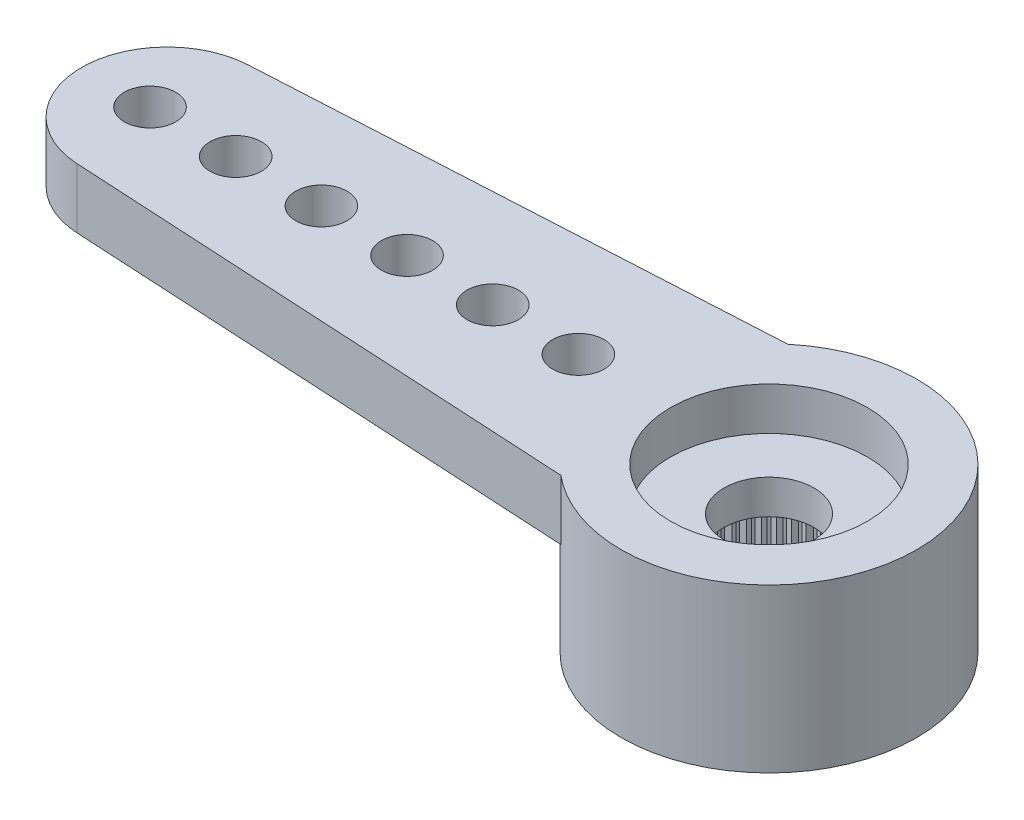
SolidWorks part; units mm, degrees
material "PVC Rígido"
ref_plane "Plano frontal" through (0, 0, 0) normal (0, 0, 1) x (1, 0, 0)
ref_plane "Plano superior" through (0, 0, 0) normal (0, 1, 0) x (1, 0, 0)
ref_plane "Plano direito" through (0, 0, 0) normal (1, 0, 0) x (0, 0, -1)
sketch "Esboço1" plane through (0, 0, 0) normal (0, 1, 0) x (1, 0, 0)
  line L0 (0, 0) -> (-14.05, 0) construction
  line L1 (-14.1591, 1.997) -> (-2.2091, 2.65)
  line L2 (-2.2091, -2.65) -> (-14.1591, -1.997)
  arc A0 (-2.2091, -2.65) -> (-2.2091, 2.65) centre (0, 0) ccw
  arc A1 (-14.1591, 1.997) -> (-14.1591, -1.997) centre (-14.05, 0) ccw
  dimension "D1" = 6.9
  dimension "D2" = 4
  dimension "D3" = 19.5
  dimension "D4" = 5.3
extrude "Ressalto-extrusão1" add sketch "Esboço1" against normal blind 1.4
sketch "Esboço2" plane through (0, -1.4, 0) normal (0, -1, 0) x (1, 0, 0)
  arc A0 (-2.2091, -2.65) -> (-2.2091, 2.65) centre (0, 0) ccw construction
  circle A1 centre (0, 0) radius 3.45
extrude "Ressalto-extrusão2" add sketch "Esboço2" along normal offset from surface (2.4 mm away) 3.8 up to face at (-7.242, 0, 0)
hole_wizard "Furo4" positions "Esboço9" profile "Esboço10" legacy end condition through all
sketch "Esboço9" plane through (0, 0, 0) normal (0, 1, 0) x (1, 0, 0)
  line L1 (-14.45, 0) -> (0, 0) construction
  arc A2 (-14.1591, 1.997) -> (-14.1591, -1.997) centre (-14.05, 0) ccw construction
  point P0 (-14.45, 0)
  point P19 (-16.05, 0)
  dimension "D1" = 1.6
sketch "Esboço10" plane through (-14.45, 0, 0) normal (1, 0, 0) x (0, 0, 1)
  line L0 (0, 0) -> (0, 3.8)
  line L1 (0, 3.8) -> (0.6, 3.8)
  line L2 (0.6, 3.8) -> (0.6, 0)
  line L3 (0.6, 0) -> (0, 0)
  line L4 (0, 110) -> (0, -10) construction
  dimension "Diameter" = 1.2
  dimension "Depth" = 3.8
pattern_linear "Padrão linear1" count 6 spacing 2 along (1, 0, 0) of "Furo4"
hole_wizard "Furo1" positions "Esboço3" profile "Esboço4" legacy
sketch "Esboço3" plane through (0, -3.8, 0) normal (0, -1, 0) x (-1, 0, 0)
  point P0 (0, 0)
sketch "Esboço4" plane through (0, -3.8, 0) normal (1, 0, 0) x (0, 0, -1)
  line L0 (0, 0) -> (0, 2)
  line L1 (0, 2) -> (2.475, 2)
  line L2 (2.475, 2) -> (2.475, 0)
  line L3 (2.475, 0) -> (0, 0)
  line L4 (0, 110) -> (0, -10) construction
  dimension "Diameter" = 4.95
  dimension "Depth" = 2
hole_wizard "Furo2" positions "Esboço5" profile "Esboço6" legacy
sketch "Esboço5" plane through (0, 0, 0) normal (0, 1, 0) x (1, 0, 0)
  point P0 (0, 0)
sketch "Esboço6" plane through (0, 0, 0) normal (1, 0, 0) x (0, 0, 1)
  line L0 (0, 0) -> (0, 1)
  line L1 (0, 1) -> (2.3, 1)
  line L2 (2.3, 1) -> (2.3, 0)
  line L3 (2.3, 0) -> (0, 0)
  line L4 (0, 110) -> (0, -10) construction
  dimension "Diameter" = 4.6
  dimension "Depth" = 1
hole_wizard "Furo3" positions "Esboço7" profile "Esboço8" legacy end condition through all
sketch "Esboço7" plane through (0, 0, 0) normal (0, 1, 0) x (1, 0, 0)
  point P0 (0, 0)
sketch "Esboço8" plane through (0, 0, 0) normal (1, 0, 0) x (0, 0, 1)
  line L0 (0, 0) -> (0, 3.8)
  line L1 (0, 3.8) -> (1.05, 3.8)
  line L2 (1.05, 3.8) -> (1.05, 0)
  line L3 (1.05, 0) -> (0, 0)
  line L4 (0, 110) -> (0, -10) construction
  dimension "Diameter" = 2.1
  dimension "Depth" = 3.8
sketch "Esboço11" plane through (0, -3.8, 0) normal (0, -1, 0) x (1, 0, 0)
  line L0 (-0.0981, 2.4731) -> (0, 2.375)
  line L1 (0, 2.375) -> (0.0981, 2.4731)
  line L2 (0, 0) -> (0, 2.475) construction
  circle A0 centre (0, 0) radius 2.375 construction
  circle A1 centre (0, 0) radius 2.475
  circle A2 centre (0, 0) radius 2.475
  point P3 (0, 0)
  point P7 (0, 0)
  point P9 (0, 2.3296)
  point P11 (0, 2.475)
  circle M6 centre (0, 0) radius 2.475
  dimension "D3" = 4.75
  dimension "D2" = 0.1
  dimension "D1" = 0
extrude "Ressalto-extrusão3" add sketch "Esboço11" against normal up to surface (2 mm away) contours L0 L1 M6
pattern_circular "PadrãoCircular1" count 60 over 360 about axis through (0, 0, 0) along (0, 1, 0) of "Ressalto-extrusão3"
